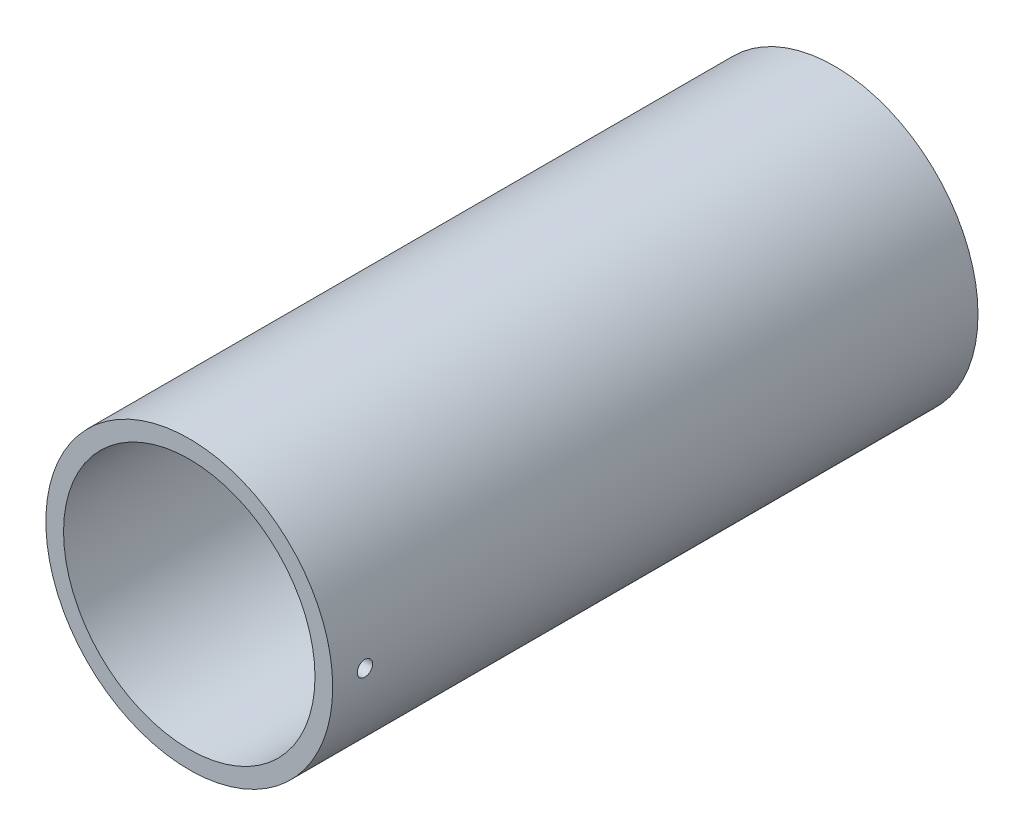
SolidWorks part; units mm, degrees
ref_plane "Front Plane" through (0, 0, 0) normal (0, 0, 1) x (1, 0, 0)
ref_plane "Top Plane" through (0, 0, 0) normal (0, 1, 0) x (1, 0, 0)
ref_plane "Right Plane" through (0, 0, 0) normal (1, 0, 0) x (0, 0, -1)
sketch "Sketch1" plane through (0, 0, 0) normal (0, 0, 1) x (1, 0, 0)
  circle A0 centre (0, 0) radius 44.45
  dimension "Pipe OD" = 88.9
extrude "Extrude-Thin1" add sketch "Sketch1" along normal mid plane 200 thin thin type one direction reverse wall 5.4864
hole_wizard "3/16 (0.1875) Diameter Hole1" positions "Sketch3" profile "Sketch2" hole size "3/16" standard "ANSI Inch"
sketch "Sketch3" plane through (0, 0, 0) normal (1, 0, 0) x (0, 0, -1)
  line L0 (-100, 44.45) -> (-100, -44.45) construction
  point P0 (-90, 0)
  dimension "D1" = 10
sketch "Sketch2" plane through (0, 0, 90) normal (0, 1, 0) x (0, 0, 1)
  line L0 (0, 0) -> (0, 44.45)
  line L1 (0, 44.45) -> (2.3812, 44.45)
  line L2 (2.3812, 44.45) -> (2.3812, 0)
  line L5 (2.3812, 0) -> (0, 0)
  line L11 (0, -6.35) -> (0, 107.95) construction
  dimension "Thru Hole Dia." = 4.7625
  dimension "Thru Hole Depth" = 44.45
